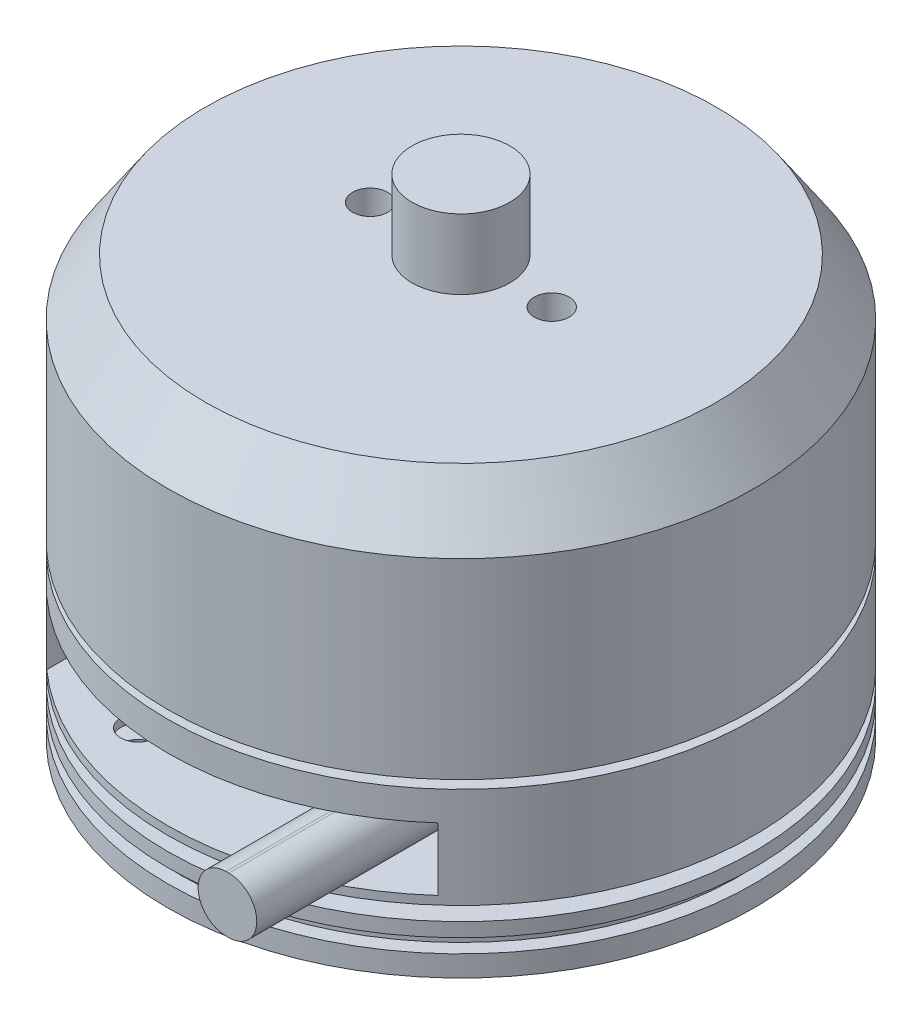
SolidWorks part; units mm, degrees
ref_plane "前视基准面" through (0, 0, 0) normal (0, 0, 1) x (1, 0, 0)
ref_plane "上视基准面" through (0, 0, 0) normal (0, 1, 0) x (1, 0, 0)
ref_plane "右视基准面" through (0, 0, 0) normal (1, 0, 0) x (0, 0, -1)
sketch "草图1" plane through (0, 0, 0) normal (0, 0, 1) x (1, 0, 0)
  line L0 (0, 0) -> (4.1, 0)
  line L1 (4.1, 0) -> (4.1, 6.7)
  line L2 (4.1, 6.7) -> (13.4, 6.7)
  line L3 (13.4, 6.7) -> (13.4, 8.7)
  line L4 (13.4, 8.7) -> (21, 8.7)
  line L5 (21, 8.7) -> (21, 10.2)
  line L6 (21, 10.2) -> (20, 10.2)
  line L7 (20, 10.2) -> (20, 11.2)
  line L8 (20, 11.2) -> (21, 11.2)
  line L9 (21, 11.2) -> (21, 12.2)
  line L10 (21, 12.2) -> (10, 12.2)
  line L11 (10, 12.2) -> (10, 13.2)
  line L12 (10, 13.2) -> (21, 13.2)
  line L13 (21, 13.2) -> (21, 20.4)
  line L14 (21, 20.4) -> (5, 20.4)
  line L15 (5, 20.4) -> (5, 21)
  line L16 (5, 21) -> (21, 21)
  line L17 (21, 21) -> (21, 34.7)
  line L18 (21, 34.7) -> (18.3, 38.7)
  line L19 (18.3, 38.7) -> (3.5, 38.7)
  line L20 (3.5, 38.7) -> (3.5, 43.7)
  line L21 (3.5, 43.7) -> (0, 43.7)
  line L22 (0, 43.7) -> (0, 0) construction
  line L23 (0, 0) -> (0, 43.7)
  dimension "D1" = 8.2
  dimension "D2" = 26.8
  dimension "D3" = 42
  dimension "D4" = 10
  dimension "D5" = 1.5
  dimension "D6" = 1
  dimension "D7" = 1
  dimension "D8" = 20
  dimension "D9" = 1
  dimension "D10" = 7.2
  dimension "D11" = 0.6
  dimension "D12" = 13.7
  dimension "D13" = 5
  dimension "D14" = 2
  dimension "D15" = 6.7
  dimension "D16" = 1
  dimension "D17" = 7
  dimension "D18" = 36.6
  dimension "D19" = 4
  dimension "D20" = 30
revolve "旋转1" add sketch "草图1" angle 360 about L22
ref_plane "基准面1" through (0, 0, 21) normal (0, 0, 1) x (1, 0, 0)
sketch "草图2" plane through (0, 0, 21) normal (0, 0, 1) x (1, 0, 0)
  line L1 (-14, 18.3) -> (14, 18.3)
  line L2 (-14, 18.3) -> (-14, 13.8)
  line L3 (-14, 13.8) -> (14, 13.8)
  line L4 (14, 18.3) -> (14, 13.8)
  line L5 (-14, 18.3) -> (14, 13.8) construction
  line L6 (-14, 13.8) -> (14, 18.3) construction
  line L7 (-21, 13.2) -> (21, 13.2) construction
  point P0 (0, 16.05)
  dimension "D1" = 28
  dimension "D2" = 4.5
  dimension "D3" = 0.6
extrude "切除-拉伸1" cut sketch "草图2" against normal blind 10
sketch "草图3" plane through (0, 0, 11) normal (0, 0, 1) x (1, 0, 0)
  line L0 (9.1851, 16.0532) -> (9.3851, 16.0532) construction
  line L1 (9.1851, 18.0532) -> (9.3851, 18.0532)
  line L2 (9.1851, 14.0532) -> (9.3851, 14.0532)
  arc A0 (9.1851, 18.0532) -> (9.1851, 14.0532) centre (9.1851, 16.0532) ccw
  arc A1 (9.3851, 14.0532) -> (9.3851, 18.0532) centre (9.3851, 16.0532) ccw
  point P2 (9.2851, 16.0532)
  dimension "D1" = 4
  dimension "D2" = 0.2
extrude "凸台-拉伸1" add sketch "草图3" along normal blind 15
hole_wizard "M3 螺纹孔1" positions "草图5" profile "草图6" tap size "M3" standard "GB"
sketch "草图5" plane through (0, 38.7, 0) normal (0, 1, 0) x (1, 0, 0)
  line L0 (0, 0) -> (0, 8.0606) construction
  point P0 (-6.5, 0)
  point P2 (6.5, 0)
  dimension "D1" = 13
sketch "草图6" plane through (-6.5, 38.7, 0) normal (1, 0, 0) x (0, 0, 1)
  line L0 (0, 0) -> (0, 4.7511)
  line L1 (0, 4.7511) -> (1.25, 4)
  line L2 (1.25, 4) -> (1.25, 0)
  line L5 (1.25, 0) -> (0, 0)
  line L10 (0, 4.7511) -> (-1.25, 4) construction
  line L11 (0, -6.35) -> (0, 107.95) construction
  dimension "螺纹孔钻头直径" = 2.5
  dimension "螺纹孔钻头深度" = 4
  dimension "导头角度" = 118
cosmetic thread "孔螺蚊线1" parameters "D1"=4, "D2"=3
cosmetic thread "孔螺蚊线2" parameters "D1"=4, "D2"=3
sketch "草图7" plane through (0, 0, 0) normal (0, 0, 1) x (1, 0, 0)
  line L0 (0, 8.7) -> (0, -54.6) construction
  line L1 (-13.4, 8.7) -> (13.4, 8.7) construction
  line L2 (0, -54.6) -> (5, -54.6)
  line L3 (5, -54.6) -> (5, -30.5)
  line L4 (5, -30.5) -> (8.275, -30.5)
  line L5 (13, -29.6) -> (13, -27.6)
  line L6 (13, -27.6) -> (21, -27.6)
  line L7 (21, -27.6) -> (21, 8.7)
  line L8 (-21, 8.7) -> (21, 8.7) construction
  line L9 (21, 8.7) -> (0, 8.7)
  line L10 (18.3, 38.7) -> (-18.3, 38.7) construction
  line L11 (13, -29.6) -> (8.275, -29.6)
  line L12 (8.275, -29.6) -> (8.275, -30.5)
  line L13 (0, 8.7) -> (0, -54.6)
  dimension "D1" = 66.3
  dimension "D2" = 2
  dimension "D3" = 0.9
  dimension "D4" = 27
  dimension "D5" = 26
  dimension "D6" = 10
  dimension "D7" = 16.55
revolve "旋转2" add sketch "草图7" angle 360 about L0
sketch "草图8" plane through (0, -54.6, 0) normal (0, -1, 0) x (1, 0, 0)
  line L0 (-3, 4) -> (3, 4)
  circle A0 centre (0, 0) radius 5 construction
  circle A1 centre (0, 0) radius 5 construction
  arc A2 (3, 4) -> (-3, 4) centre (0, 0) ccw
  dimension "D1" = 4
extrude "切除-拉伸2" cut sketch "草图8" against normal blind 20
hole_wizard "M4 螺纹孔1" positions "草图10" profile "草图9" tap size "M4" standard "GB"
sketch "草图10" plane through (0, -27.6, 0) normal (0, -1, 0) x (-1, 0, 0)
  circle A0 centre (0, 0) radius 17.5
  point P5 (0, -17.5)
  point P7 (-17.5, 0)
  point P9 (0, 17.5)
  point P11 (17.5, 0)
  dimension "D1" = 35
sketch "草图9" plane through (-17.5, -27.6, 0) normal (1, 0, 0) x (0, 0, -1)
  line L0 (0, 0) -> (0, 11.0914)
  line L1 (0, 11.0914) -> (1.65, 10.1)
  line L2 (1.65, 10.1) -> (1.65, 0)
  line L5 (1.65, 0) -> (0, 0)
  line L10 (0, 11.0914) -> (-1.65, 10.1) construction
  line L11 (0, -6.35) -> (0, 107.95) construction
  dimension "螺纹孔钻头直径" = 3.3
  dimension "螺纹孔钻头深度" = 10.1
  dimension "导头角度" = 118
cosmetic thread "孔螺蚊线3" parameters "D1"=8, "D2"=4
cosmetic thread "孔螺蚊线4" parameters "D1"=8, "D2"=4
cosmetic thread "孔螺蚊线5" parameters "D1"=8, "D2"=4
cosmetic thread "孔螺蚊线6" parameters "D1"=8, "D2"=4
sketch "草图11" plane through (0, 0, 4) normal (0, 0, 1) x (1, 0, 0)
  line L0 (0, -54.6) -> (0, -36.079) construction
  line L1 (-3, -54.6) -> (3, -54.6) construction
  line L2 (-13.929, -44.6) -> (10.5915, -44.6) construction
  circle A0 centre (0, -44.6) radius 1.9071
  dimension "D1" = 10
hole_wizard "M3 螺纹孔2" positions "3D草图1" profile "草图12" tap size "M3" standard "GB" end condition through all
sketch3d "3D草图1"
  point P0 (0, -44.6, 4)
sketch "草图12" plane through (0, -44.6, 4) normal (1, 0, 0) x (0, -1, 0)
  line L0 (0, 0) -> (0, 25)
  line L1 (0, 25) -> (1.25, 25)
  line L2 (1.25, 25) -> (1.25, 0)
  line L5 (1.25, 0) -> (0, 0)
  line L11 (0, -6.35) -> (0, 107.95) construction
  dimension "螺纹线主直径" = 2.5
  dimension "通孔螺纹孔钻头深度" = 25
sketch "草图15" plane through (0, -54.6, 0) normal (0, -1, 0) x (1, 0, 0)
  point P0 (0, 0)
hole_wizard "M5 螺纹孔1" positions "3D草图5" profile "草图16" tap size "M5" standard "GB"
sketch3d "3D草图5"
  point P0 (0, -54.6, 0)
  point P3 (0, -54.6, 0)
sketch "草图16" plane through (0, -54.6, 0) normal (1, 0, 0) x (0, 0, -1)
  line L0 (0, 0) -> (0, 15.2618)
  line L1 (0, 15.2618) -> (2.1, 14)
  line L2 (2.1, 14) -> (2.1, 0)
  line L5 (2.1, 0) -> (0, 0)
  line L10 (0, 15.2618) -> (-2.1, 14) construction
  line L11 (0, -6.35) -> (0, 107.95) construction
  dimension "螺纹孔钻头直径" = 4.2
  dimension "螺纹孔钻头深度" = 14
  dimension "导头角度" = 118
cosmetic thread "孔螺蚊线7" parameters "D1"=10, "D2"=5.2
cosmetic thread "孔螺蚊线8" parameters "D1"=10, "D2"=5.2
sketch "草图17" plane through (0, 0, 0) normal (1, 0, 0) x (0, 0, -1)
  line L0 (18.3, 38.7) -> (-18.3, 38.7) construction
  line L1 (-35.0949, 8.7) -> (38.6801, 8.7)
  line L2 (-35.0949, 8.7) -> (-35.0949, -74.5333)
  line L3 (-35.0949, -74.5333) -> (38.6801, -74.5333)
  line L4 (38.6801, 8.7) -> (38.6801, -74.5333)
  line L5 (1.7926, -74.5333) -> (1.7926, 8.7) construction
  line L6 (-35.0949, -32.9166) -> (38.6801, -32.9166) construction
  point P76 (1.7926, -32.9166)
  dimension "D1" = 30
extrude "切除-拉伸3" cut sketch "草图17" against normal through all both and the other way through all
sketch "草图18" plane through (0, 8.7, 0) normal (0, -1, 0) x (1, 0, 0)
  circle A0 centre (0, 0) radius 13.4
  dimension "D1" = 26.8
extrude "凸台-拉伸2" add sketch "草图18" along normal blind 2
sketch "草图19" plane through (0, 6.7, 0) normal (0, -1, 0) x (1, 0, 0)
  circle A0 centre (0, 0) radius 5.75
  dimension "D1" = 11.5
extrude "凸台-拉伸3" add sketch "草图19" along normal blind 6.7
sketch "草图20" plane through (0, 8.7, 0) normal (0, -1, 0) x (1, 0, 0)
  line L0 (-7.1179, 15.987) -> (0, 0) construction
  line L1 (0, 0) -> (0, 9.9342) construction
  line L2 (0, 0) -> (-7.1179, 15.987) construction
  circle A0 centre (-7.1179, 15.987) radius 1.25
  circle A1 centre (15.987, 7.1179) radius 1.25
  circle A2 centre (7.1179, -15.987) radius 1.25
  circle A3 centre (-15.987, -7.1179) radius 1.25
  dimension "D3" = 2.5
  dimension "D1" = 17.5
  dimension "D2" = 24
  dimension "D5" = 4
extrude "切除-拉伸4" cut sketch "草图20" against normal blind 8
cosmetic thread "装饰螺纹线5" parameters "D2"=3
cosmetic thread "装饰螺纹线6" parameters "D2"=3
cosmetic thread "装饰螺纹线7" parameters "D2"=3
cosmetic thread "装饰螺纹线8" parameters "D2"=3
cosmetic thread "装饰螺纹线9" parameters "D2"=3
cosmetic thread "装饰螺纹线10" parameters "D2"=3
cosmetic thread "装饰螺纹线11" parameters "D2"=3
cosmetic thread "装饰螺纹线12" parameters "D2"=3
